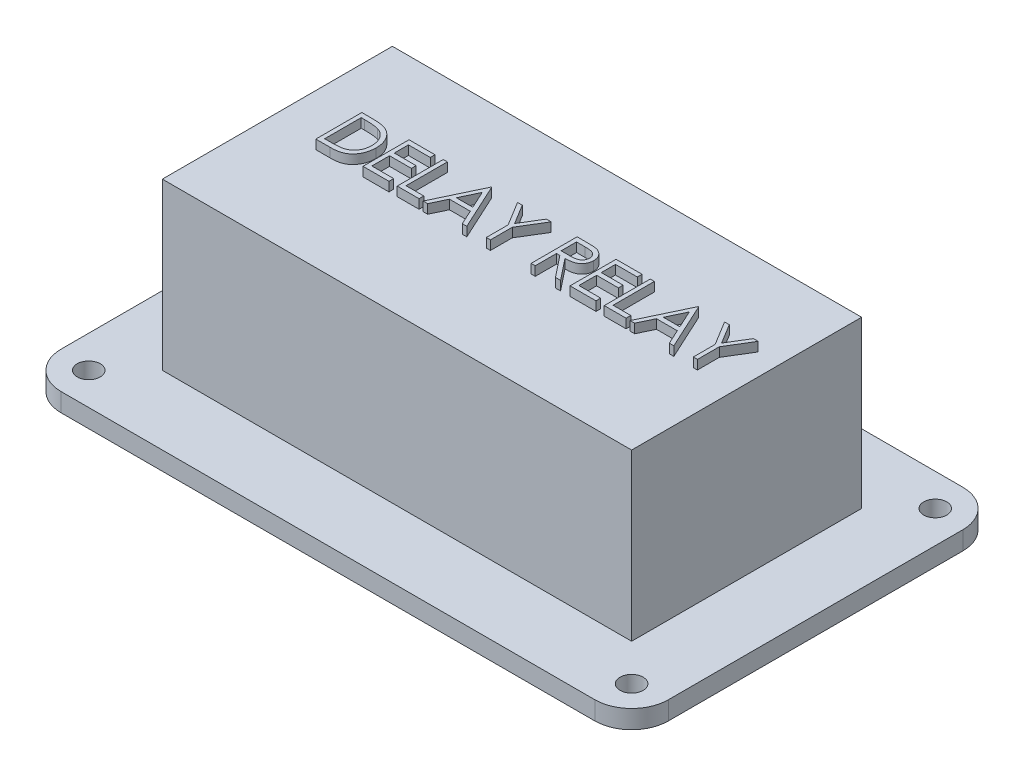
SolidWorks part; units mm, degrees
ref_plane "Front Plane" through (0, 0, 0) normal (0, 0, 1) x (1, 0, 0)
ref_plane "Top Plane" through (0, 0, 0) normal (0, 1, 0) x (1, 0, 0)
ref_plane "Right Plane" through (0, 0, 0) normal (1, 0, 0) x (0, 0, -1)
sketch "Sketch1" plane through (0, 0, 0) normal (0, 1, 0) x (1, 0, 0)
  line L1 (-33, -20) -> (33, -20)
  line L2 (-33, -20) -> (-33, 20)
  line L3 (-33, 20) -> (33, 20)
  line L4 (33, -20) -> (33, 20)
  line L5 (-33, -20) -> (33, 20) construction
  line L6 (-33, 20) -> (33, -20) construction
  point P0 (0, 0)
  dimension "D1" = 66
  dimension "D2" = 40
extrude "Boss-Extrude1" add sketch "Sketch1" along normal blind 2 contours L3 L4 L1 L2
fillet "Fillet1" radius 4 4 edges at (33, 1, 20) (33, 1, -20) (-33, 1, -20) (-33, 1, 20)
hole_wizard "Tap Drill for M3x0.5 Tap1" positions "Sketch2" profile "Sketch3" hole size "M3x0.5" standard "ANSI Metric" end condition through all
sketch "Sketch2" plane through (0, 2, 0) normal (0, 1, 0) x (1, 0, 0)
  line L0 (-29, 20) -> (29, 20) construction
  line L1 (-33, -16) -> (-33, 16) construction
  point P0 (-29.5, 16.5)
  point P2 (29.5, 16.5)
  point P4 (29.5, -16.5)
  point P6 (-29.5, -16.5)
  dimension "D1" = 33
  dimension "D2" = 59
  dimension "D3" = 3.5
  dimension "D4" = 3.5
sketch "Sketch3" plane through (-29.5, 2, -16.5) normal (1, 0, 0) x (0, 0, 1)
  line L0 (0, 0) -> (0, 2)
  line L1 (0, 2) -> (1.25, 2)
  line L2 (1.25, 2) -> (1.25, 0)
  line L5 (1.25, 0) -> (0, 0)
  line L11 (0, -6.35) -> (0, 107.95) construction
  dimension "Thru Hole Dia." = 2.5
  dimension "Thru Hole Depth" = 2
sketch "Sketch4" plane through (0, 2, 0) normal (0, 1, 0) x (1, 0, 0)
  line L26 (25.5, -12.5) -> (25.5, 12.5)
  line L27 (-25.5, -12.5) -> (25.5, -12.5)
  line L28 (-25.5, 12.5) -> (-25.5, -12.5)
  line L29 (25.5, 12.5) -> (-25.5, 12.5)
  line L30 (25.5, -12.5) -> (25.5, 12.5)
  line L31 (-25.5, -12.5) -> (25.5, -12.5)
  line L32 (-25.5, 12.5) -> (-25.5, -12.5)
  line L33 (25.5, 12.5) -> (-25.5, 12.5)
  dimension "D1" = 7.5
extrude "Boss-Extrude2" add sketch "Sketch4" along normal blind 18
sketch "Sketch5" plane through (0, 20, 0) normal (0, 1, 0) x (1, 0, 0)
  text T0 "DELAY RELAY" font "Century Gothic" height 5
extrude "Boss-Extrude3" add sketch "Sketch5" along normal blind 1
